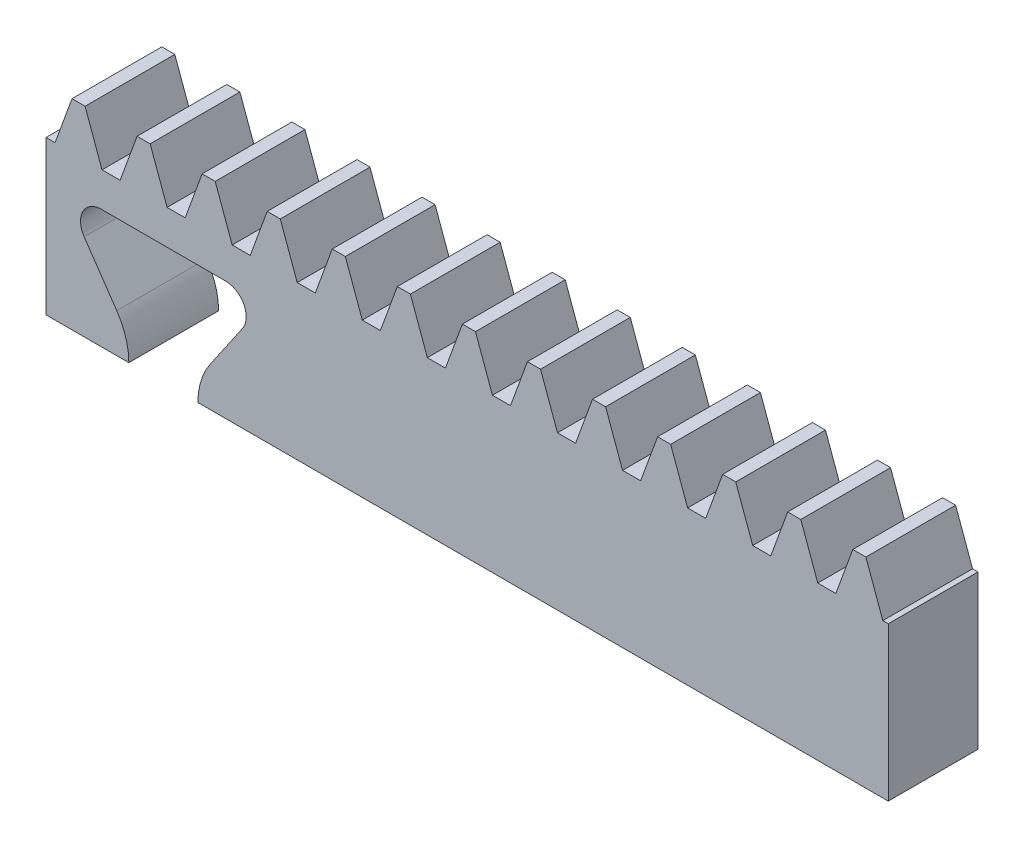
SolidWorks part; units mm, degrees
extrude "Blank" add sketch "BlankSke" against normal blind 6.5
sketch "BlankSke" plane through (0, 0, 0) normal (0, 0, 1) x (1, 0, 0)
  line L1 (0, 0) -> (61, 0)
  line L2 (0, 0) -> (0, 14.5)
  line L3 (0, 14.5) -> (61, 14.5)
  line L4 (61, 0) -> (61, 14.5)
  dimension "Length" = 61
  dimension "Blank_height" = 14.5
ref_plane "Plane1" through (0, 0, 0) normal (0, 0, 1) x (1, 0, 0)
ref_plane "Plane2" through (0, 0, 0) normal (0, 1, 0) x (1, 0, 0)
ref_plane "Plane3" through (0, 0, 0) normal (1, 0, 0) x (0, 0, -1)
other "Configuration Table"
sketch "HoldingSke" plane through (0, 0, 0) normal (0, 1, 0) x (1, 0, 0)
  line L0 (0, 0) -> (0.0928, 0.6602)
  line L1 (-15, 0) -> (100, 0) construction
  line L2 (0, 0) -> (-2.1039, 2.3779)
  line L3 (0, 0) -> (-11.863, 4.5341)
  line L4 (0, 0) -> (8.3795, 2.0892)
  line L5 (0, 0) -> (-23.7986, -8.8762)
  line L6 (0, 0) -> (-10.5278, -7.1032)
  line L9 (-71.009, 38.7566) -> (-13.6877, 59.6198)
  line L10 (-76.2, 3.8779) -> (-63.2, 3.8779)
  line L11 (0, 0) -> (-6.5, 0)
  line L12 (-76.2, 101.6) -> (-76.147, 101.6)
  line L13 (24.9733, 27.94) -> (52.9518, 28.4284)
  line L14 (24.9733, 27.94) -> (24.9743, 27.94)
  line L15 (24.9733, 27.94) -> (100.4006, 29.5858)
  circle A0 centre (0, 0) radius 19.05
  circle A1 centre (0, 0) radius 6.5
  circle A2 centre (0, 0) radius 12.7
  dimension "MPH" = 13
  dimension "Diameter" = 38.1
  dimension "Num_teeth" = 14
  dimension "Pitch" = 0.6667
  dimension "Show_teeth" = 998
  dimension "Thickness" = 12.7
  dimension "Ap" = 20
  dimension "Pitch_height" = 13
  dimension "Width" = 6.5
  dimension "Backlash" = 0.053
  dimension "Addendum_fac" = 1
  dimension "Dedendum_fac" = 1.25
  dimension "Clearance_fac" = 0.25
  dimension "Dedendum_add" = 0.001
  dimension "Length" = 61
  dimension "Module" = 1.5
sketch "TooCutSkeIll" plane through (0, 0, 0) normal (0, 0, 1) x (1, 0, 0)
  line L0 (-1.8687, 14.4605) -> (-0.7447, 11.3724)
  line L1 (-0.3914, 11.125) -> (0.3914, 11.125)
  line L2 (0.7447, 11.3724) -> (1.8687, 14.4605)
  line L3 (61, 14.5) -> (0, 14.5) construction
  line L4 (0, 0) -> (0, 64.897) construction
  line L5 (-13.208, 13) -> (12.954, 13) construction
  line L6 (0, 0) -> (61, 0) construction
  line L7 (1.3371, 13) -> (1.3371, 48.7463) construction
  line L8 (-1.3371, 13) -> (-1.3371, 48.7463) construction
  line L9 (1.9251, 14.5) -> (1.9251, 14.5254)
  line L10 (-1.9251, 14.5) -> (-1.9251, 14.5254)
  line L11 (-1.9251, 14.5254) -> (1.9251, 14.5254)
  arc A0 (0.3914, 11.125) -> (0.7447, 11.3724) centre (0.3914, 11.501) ccw
  arc A1 (-0.7447, 11.3724) -> (-0.3914, 11.125) centre (-0.3914, 11.501) ccw
  arc A2 (1.9251, 14.5) -> (1.8687, 14.4605) centre (1.9251, 14.44) ccw
  arc A3 (-1.8687, 14.4605) -> (-1.9251, 14.5) centre (-1.9251, 14.44) ccw
  dimension "Pitch_height" = 13
  dimension "Addendum_plus" = 1.5254
  dimension "Pressure_angle" = 20
  dimension "Gap_width" = 2.6742
  dimension "Dedendum" = 1.875
extrude "ToothCutIll" [suppressed] cut sketch "TooCutSkeIll" against normal through all
sketch "TooCutSkeSim" plane through (0, 0, 0) normal (0, 0, 1) x (1, 0, 0)
  line L0 (0.6547, 11.125) -> (-0.6547, 11.125)
  line L1 (1.8923, 14.5254) -> (0.6547, 11.125)
  line L2 (0, 17.4625) -> (0, 53.467) construction
  line L3 (1.8923, 14.5254) -> (-1.8923, 14.5254)
  line L6 (-1.8923, 14.5254) -> (-0.6547, 11.125)
  line L9 (-1.3371, 13) -> (1.3371, 13) construction
  line L10 (0, 0) -> (61, 0) construction
  line L11 (1.3371, 13) -> (1.3371, 53.467) construction
  line L12 (-1.3371, 13) -> (-1.3371, 53.467) construction
  dimension "Pitch_height" = 13
  dimension "Addendum_plus" = 1.5254
  dimension "Pressure_angle" = 20
  dimension "Gap_width" = 2.6742
  dimension "Dedendum" = 1.875
extrude "ToothCutSim" cut sketch "TooCutSkeSim" against normal through all
pattern_linear "TeethCuts" count 14 spacing 4.7124 along (1, 0, 0) of "ToothCutIll", "ToothCutSim"
sketch "Sketch2" plane through (0, 0, 0) normal (0, 0, 1) x (1, 0, 0)
  line L0 (8.5, 0) -> (8.5, 7.8042) construction
  line L1 (0, 0) -> (61, 0) construction
  line L2 (0, 11.125) -> (0, 0) construction
  line L3 (13, 8.625) -> (4, 8.625)
  line L4 (2.7622, 6.2778) -> (5.1261, 2.8241)
  line L5 (14.2378, 6.2778) -> (11.8739, 2.8241)
  line L6 (11, 0) -> (6, 0)
  line L7 (8.7701, 11.125) -> (10.0794, 11.125) construction
  arc A0 (4, 8.625) -> (2.7622, 6.2778) centre (4, 7.125) ccw
  arc A1 (13, 8.625) -> (14.2378, 6.2778) centre (13, 7.125) cw
  arc A2 (6, 0) -> (5.1261, 2.8241) centre (1, 0) ccw
  arc A3 (11, 0) -> (11.8739, 2.8241) centre (16, 0) cw
  point P9 (8.5, 8.625)
  point P24 (8.5, 0)
  dimension "D4" = 1.5
  dimension "D6" = 5
  dimension "D1" = 8.5
  dimension "D2" = 9
  dimension "D3" = 5
  dimension "D5" = 2.5
  dimension "D7" = 8.625
extrude "Dovetail" cut sketch "Sketch2" against normal up to surface (6.5 mm away) up to face at (30.6212, 12.2946, -6.5)
equation "' \"Module@HoldingSke\" = 6.35"
equation "' \"Num_teeth@HoldingSke\" = 12"
equation "' \"Ap@HoldingSke\" =  20"
equation "' \"Ap@HoldingSke\" = 20"
equation "' \"Width@HoldingSke\" = 0.25 * 25.4"
equation "' \"Show_teeth@HoldingSke\" = 500"
equation "' \"Backlash@HoldingSke\" = 0.009 * 25.4"
equation "' \"Addendum_fac@HoldingSke\" = 1.0"
equation "' \"Dedendum_fac@HoldingSke\" = 1.25"
equation "' \"Dedendum_add@HoldingSke\" = 0.00005 * 25.4"
equation "' \"Clearance_fac@HoldingSke\" = 0.25"
equation "' \"Pitch_height@HoldingSke\" = 1 * 25.4"
equation "' \"Length@HoldingSke\" = 4.71 * 25.4"
equation "\"Pitch@HoldingSke\" = 1 / \"Module@HoldingSke\""
equation "\"MPH@HoldingSke\" = \"Dedendum_fac@HoldingSke\" / \"Pitch@HoldingSke\" + 2 * \"Dedendum_add@HoldingSke\" + 0.002 * 25.4"
equation "\"MPH@HoldingSke\" = ((sgn( \"MPH@HoldingSke\" - \"Pitch_height@HoldingSke\")+1)*( \"MPH@HoldingSke\" - \"Pitch_height@HoldingSke\"))/2 + \"Pitch_height@HoldingSke\""
equation "\"Blank_height@BlankSke\" = \"Pitch_height@HoldingSke\" + \"Addendum_fac@HoldingSke\"  / \"Pitch@HoldingSke\" "
equation "\"Length@BlankSke\" =  \"Length@HoldingSke\""
equation "\"Face_width@Blank\" = \"Width@HoldingSke\""
equation "\"Pressure_angle@TooCutSkeIll\" = \"Ap@HoldingSke\""
equation "\"Addendum_plus@TooCutSkeIll\" =  \"Addendum_fac@HoldingSke\"  / \"Pitch@HoldingSke\" + 0.001 *25.4"
equation "\"Dedendum@TooCutSkeIll\" = \"Dedendum_fac@HoldingSke\"  / \"Pitch@HoldingSke\""
equation "\"Pitch_height@TooCutSkeIll\" =  \"MPH@HoldingSke\""
equation "\"Gap_width@TooCutSkeIll\" = 3.14159265 / 2 / \"Pitch@HoldingSke\" + 6 * \"Backlash@HoldingSke\""
equation "\"Pressure_angle@TooCutSkeSim\" = \"Ap@HoldingSke\""
equation "\"Addendum_plus@TooCutSkeSim\" =  \"Addendum_fac@HoldingSke\"  / \"Pitch@HoldingSke\" + 0.001 * 25.4"
equation "\"Dedendum@TooCutSkeSim\" = \"Dedendum_fac@HoldingSke\"  / \"Pitch@HoldingSke\""
equation "\"Pitch_height@TooCutSkeSim\" =  \"MPH@HoldingSke\""
equation "\"Gap_width@TooCutSkeSim\" = 3.14159265 / 2 / \"Pitch@HoldingSke\" + 6 * \"Backlash@HoldingSke\""
equation "\"Root_fillet@TooCutSkeIll\" = \"Clearance_fac@HoldingSke\" / \"Pitch@HoldingSke\" + \"Dedendum_add@HoldingSke\""
equation "\"Break_rad@TooCutSkeIll\" = 0.02 / \"Pitch@HoldingSke\" * 2"
equation "\"Linear_pitch@TeethCuts\" = 3.14159265 / \"Pitch@HoldingSke\""
equation "\"Num_teeth@HoldingSke\" = int( ( \"Length@HoldingSke\" + 0 ) / (3.14159265 / \"Pitch@HoldingSke\")) + 0.9999  + 1"
equation " \"Num_teeth@TeethCuts\" = int( \"Show_teeth@HoldingSke\" ) + 1"
equation " \"Num_teeth@TeethCuts\" = ((sgn( \"Num_teeth@TeethCuts\" - \"Num_teeth@HoldingSke\" )-1)*( \"Num_teeth@TeethCuts\" - \"Num_teeth@HoldingSke\" ))/-2+ \"Num_teeth@HoldingSke\""
equation " \"Num_teeth@TeethCuts\" = ((sgn( \"Num_teeth@TeethCuts\" - 2.0)+1)*( \"Num_teeth@TeethCuts\" - 2.0))/2 +2.0"
